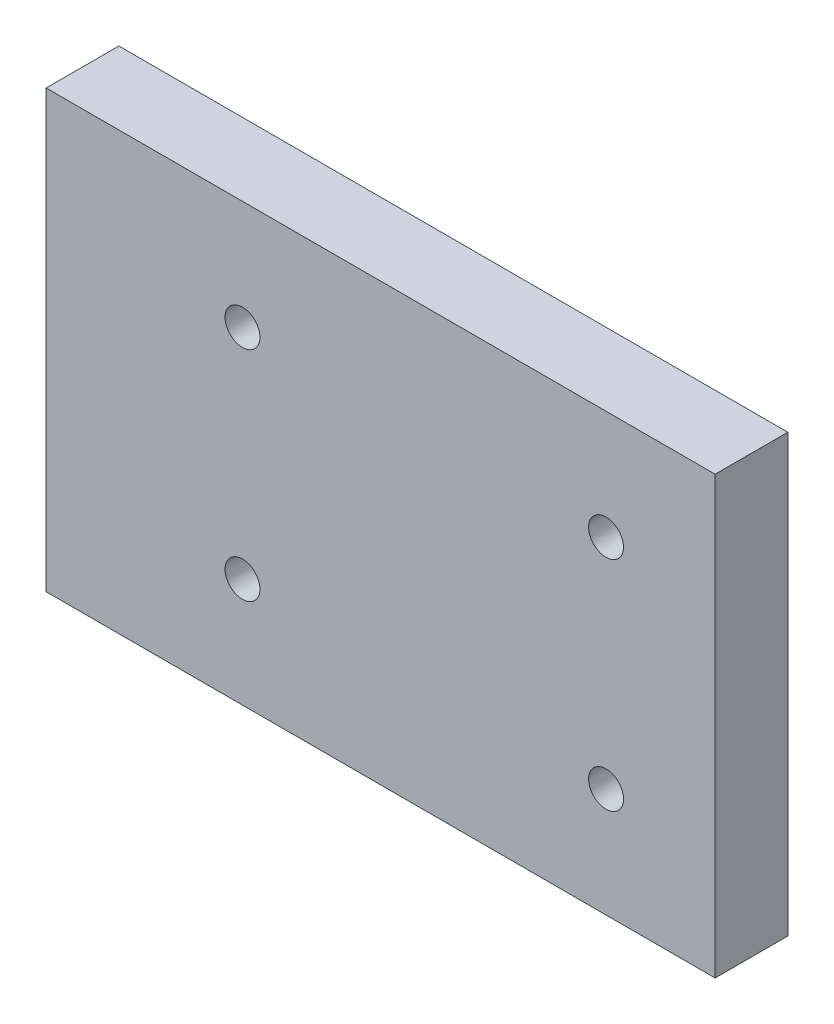
SolidWorks part; units mm, degrees
ref_plane "Front Plane" through (0, 0, 0) normal (0, 0, 1) x (1, 0, 0)
ref_plane "Top Plane" through (0, 0, 0) normal (0, 1, 0) x (1, 0, 0)
ref_plane "Right Plane" through (0, 0, 0) normal (1, 0, 0) x (0, 0, -1)
sketch "Sketch1" plane through (0, 0, 0) normal (0, 0, 1) x (1, 0, 0)
  line L1 (31.75, 18.8661) -> (-26.67, 18.8661)
  line L2 (31.75, 18.8661) -> (31.75, 56.9661)
  line L3 (31.75, 56.9661) -> (-26.67, 56.9661)
  line L4 (-26.67, 18.8661) -> (-26.67, 56.9661)
  line L5 (0, 0) -> (-1.27, 1.27) construction
  line L6 (1.27, 1.27) -> (0, 0) construction
  line L7 (-26.67, 37.9161) -> (31.75, 37.9161) construction
  line L9 (2.54, 56.9661) -> (2.54, 18.8661) construction
  circle A0 centre (22.225, 47.4411) radius 1.524
  circle A1 centre (22.225, 28.3911) radius 1.524
  circle A2 centre (-9.525, 47.4411) radius 1.524
  circle A3 centre (-9.525, 28.3911) radius 1.524
  point P0 (0, 0)
  point P10 (-13.97, -12.7)
  dimension "D3" = 9.525
  dimension "D1" = 58.42
  dimension "D2" = 19.05
  dimension "D4" = 2
  dimension "D8" = 38.1
extrude "Boss-Extrude1" add sketch "Sketch1" along normal blind 6.35
